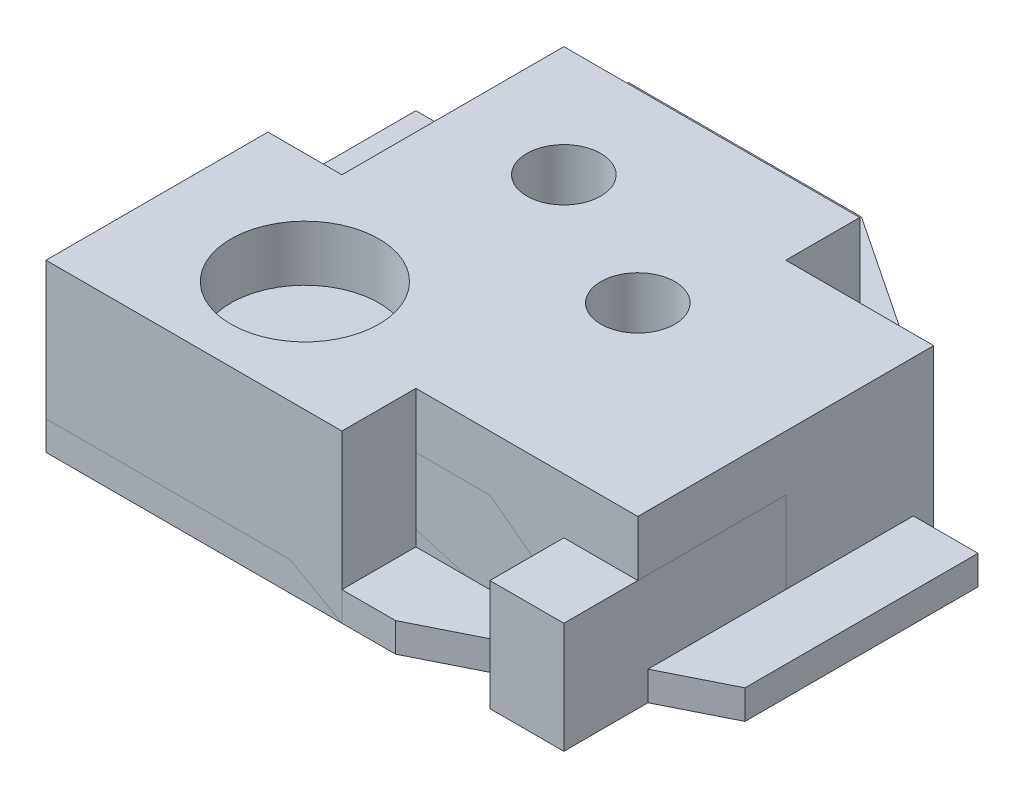
SolidWorks part; units mm, degrees
ref_plane "Front Plane" through (0, 0, 0) normal (0, 0, 1) x (1, 0, 0)
ref_plane "Top Plane" through (0, 0, 0) normal (0, 1, 0) x (1, 0, 0)
ref_plane "Right Plane" through (0, 0, 0) normal (1, 0, 0) x (0, 0, -1)
sketch "Sketch2" plane through (0, 0, 0) normal (0, 1, 0) x (1, 0, 0)
  line L0 (0, 0) -> (0, 63.5)
  line L1 (0, 63.5) -> (50.8, 63.5)
  line L2 (0, 0) -> (12.7, 0)
  line L3 (12.7, 0) -> (12.7, 12.7)
  line L4 (12.7, 12.7) -> (76.2, 12.7)
  line L5 (76.2, 12.7) -> (76.2, 0)
  line L6 (76.2, 0) -> (88.9, 0)
  line L7 (88.9, 0) -> (88.9, 38.1)
  line L8 (88.9, 38.1) -> (50.8, 63.5)
  circle A0 centre (25.4, 38.1) radius 6.35
  circle A1 centre (57.15, 38.1) radius 6.35
  dimension "D8" = 12.7
  dimension "D11" = 12.7
  dimension "D1" = 63.5
  dimension "D2" = 50.8
  dimension "D3" = 12.7
  dimension "D4" = 12.7
  dimension "D5" = 63.5
  dimension "D6" = 88.9
  dimension "D7" = 38.1
  dimension "D9" = 25.4
  dimension "D10" = 25.4
  dimension "D12" = 31.75
extrude "Boss-Extrude1" add sketch "Sketch2" along normal blind 19.05
sketch "Sketch3" plane through (0, 0, 0) normal (0, 1, 0) x (1, 0, 0)
  line L0 (0, 0) -> (0, 38.1)
  line L1 (0, 38.1) -> (12.7, 38.1)
  line L2 (0, 0) -> (50.8, 0)
  line L3 (50.8, 0) -> (50.8, 12.7)
  line L4 (50.8, 12.7) -> (88.9, 12.7)
  line L5 (88.9, 12.7) -> (88.9, 63.5)
  line L6 (88.9, 63.5) -> (63.5, 63.5)
  line L7 (63.5, 63.5) -> (63.5, 76.2)
  line L8 (63.5, 76.2) -> (12.7, 76.2)
  line L9 (12.7, 38.1) -> (12.7, 76.2)
  circle A0 centre (25.4, 19.05) radius 12.7
  circle A1 centre (31.75, 57.15) radius 6.35
  circle A2 centre (57.15, 44.45) radius 6.35
  dimension "D9" = 25.4
  dimension "D12" = 19.05
  dimension "D14" = 12.7
  dimension "D15" = 12.7
  dimension "D1" = 38.1
  dimension "D2" = 12.7
  dimension "D3" = 50.8
  dimension "D4" = 12.7
  dimension "D5" = 88.9
  dimension "D6" = 50.8
  dimension "D7" = 76.2
  dimension "D8" = 12.7
  dimension "D10" = 25.4
  dimension "D11" = 19.05
  dimension "D13" = 19.05
  dimension "D16" = 31.75
  dimension "D17" = 44.45
extrude "Boss-Extrude2" add sketch "Sketch3" along normal blind 28.575 separate body
sketch "Sketch5" plane through (0, 0, 0) normal (0, 1, 0) x (1, 0, 0)
  line L0 (0, 0) -> (0, 100)
  line L1 (0, 100) -> (40, 100)
  line L2 (0, 0) -> (60, 0)
  line L3 (60, 0) -> (100, 20)
  line L4 (100, 20) -> (100, 60)
  line L5 (100, 60) -> (70, 60)
  line L6 (70, 60) -> (70, 80)
  line L7 (70, 80) -> (40, 100)
  circle A0 centre (20, 80) radius 10
  circle A1 centre (20, 20) radius 10
  circle A2 centre (75, 30) radius 10
  point P15 (0, 0)
  dimension "D9" = 20
  dimension "D10" = 20
  dimension "D11" = 20
  dimension "D1" = 100
  dimension "D2" = 40
  dimension "D3" = 60
  dimension "D4" = 100
  dimension "D5" = 60
  dimension "D6" = 20
  dimension "D7" = 20
  dimension "D8" = 70
  dimension "D12" = 60
  dimension "D13" = 20
  dimension "D14" = 20
  dimension "D15" = 75
  dimension "D16" = 30
extrude "Boss-Extrude3" add sketch "Sketch5" along normal blind 5 separate body
